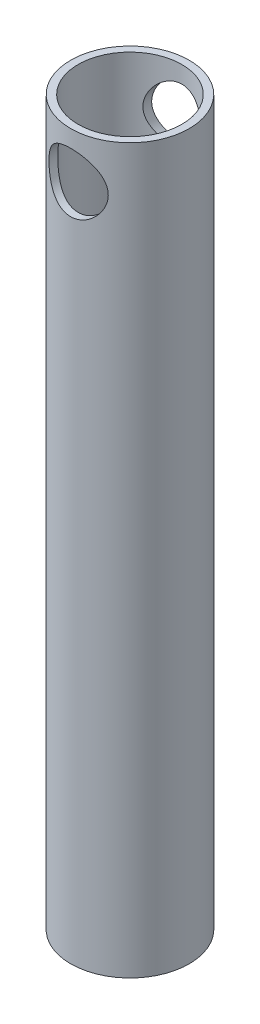
SolidWorks part; units mm, degrees
material "Plain Carbon Steel"
ref_plane "Front Plane" through (0, 0, 0) normal (0, 0, 1) x (1, 0, 0)
ref_plane "Top Plane" through (0, 0, 0) normal (0, 1, 0) x (1, 0, 0)
ref_plane "Right Plane" through (0, 0, 0) normal (1, 0, 0) x (0, 0, -1)
sketch "Sketch1" plane through (0, 0, 0) normal (0, 1, 0) x (1, 0, 0)
  circle A0 centre (0, 0) radius 12.7
  dimension "D1" = 25.4
extrude "Extrude-Thin1" add sketch "Sketch1" along normal blind 155 thin thin type one direction reverse wall 1.5875
sketch "Sketch2" plane through (0, 0, 0) normal (0, 0, 1) x (1, 0, 0)
  line L0 (0, 0) -> (0, 155) construction
  circle A0 centre (0, 145) radius 6.35
  dimension "D1" = 12.7
  dimension "D2" = 10
extrude "Cut-Extrude1" cut sketch "Sketch2" against normal through all and the other way through all
